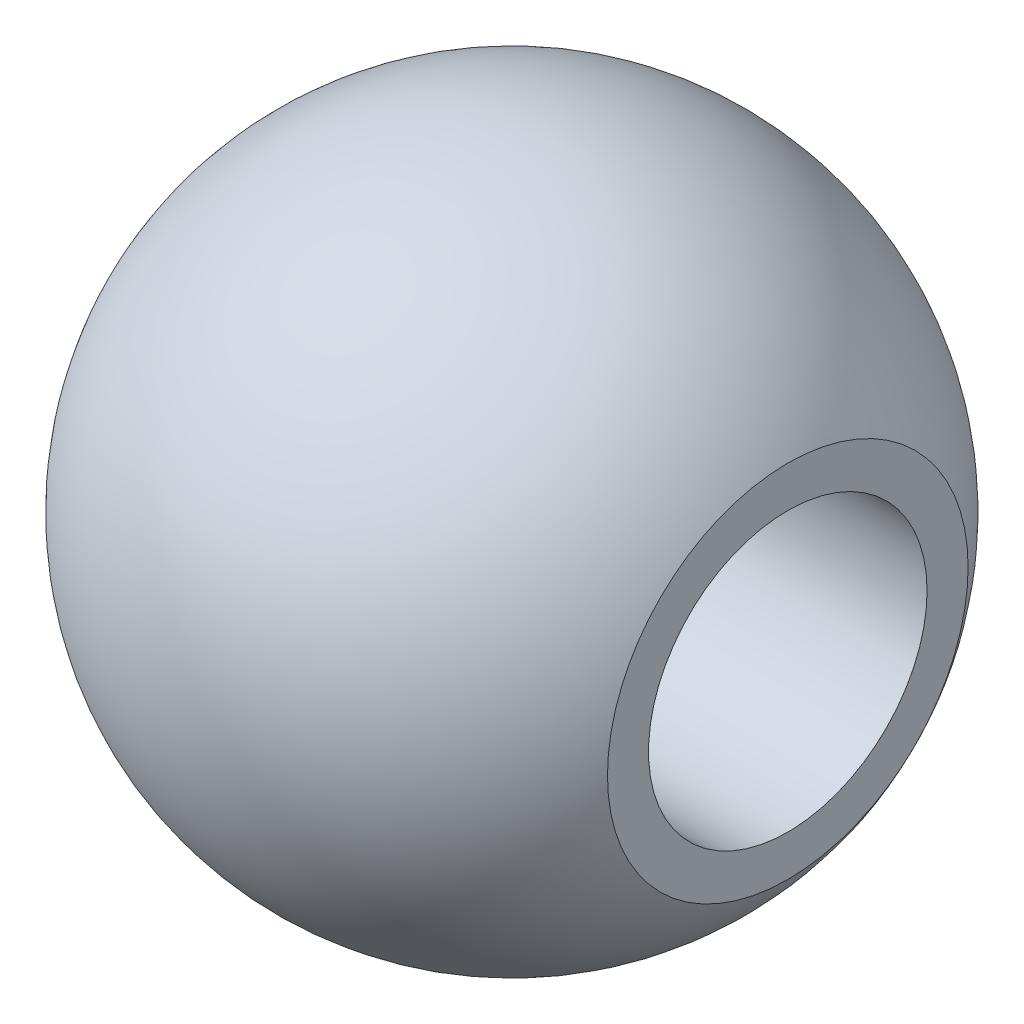
SolidWorks part; units mm, degrees
ref_plane "Front Plane" through (0, 0, 0) normal (0, 0, 1) x (1, 0, 0)
ref_plane "Top Plane" through (0, 0, 0) normal (0, 1, 0) x (1, 0, 0)
ref_plane "Right Plane" through (0, 0, 0) normal (1, 0, 0) x (0, 0, -1)
sketch "Sketch1" plane through (0, 0, 0) normal (1, 0, 0) x (0, 0, -1)
  circle A0 centre (0, 0) radius 11.2
  circle A1 centre (0, 0) radius 13.5
  dimension "D1" = 22.4
  dimension "D2" = 27
extrude "Boss-Extrude1" add sketch "Sketch1" along normal blind 45
sketch "Sketch2" plane through (0, 0, 0) normal (0, 0, 1) x (1, 0, 0)
  line L0 (5, 12.6) -> (5, 9.6)
  line L1 (5, 9.6) -> (8, 9.6)
  line L2 (0, 13.5) -> (0, -13.5) construction
  arc A0 (5, 12.6) -> (8, 9.6) centre (5, 9.6) cw
  dimension "D1" = 3
  dimension "D2" = 12.6
  dimension "D3" = 5
revolve "Cut-Revolve1" cut sketch "Sketch2" angle 360 about L0
pattern_circular "CirPattern1" count 8 over 360 about axis through (0, 0, 0) along (1, 0, 0) of "Cut-Revolve1"
pattern_linear "LPattern1" count 2 spacing 20 along (1, 0, 0) of "CirPattern1", "Cut-Revolve1"
fillet "Fillet1" radius 2 1 edges at (0, 0, -11.2)
sketch "Sketch3" plane through (0, 0, 0) normal (0, 0, 1) x (1, 0, 0)
  line L0 (0, 0) -> (123.7677, 0) construction
  line L1 (0, 13.5) -> (45, 13.5)
  line L2 (45, 13.5) -> (45, 14.5)
  arc A0 (0, 13.5) -> (45, 14.5) centre (22.8111, 0) cw
  dimension "D1" = 1
revolve "Revolve1" add sketch "Sketch3" angle 360 about L0
